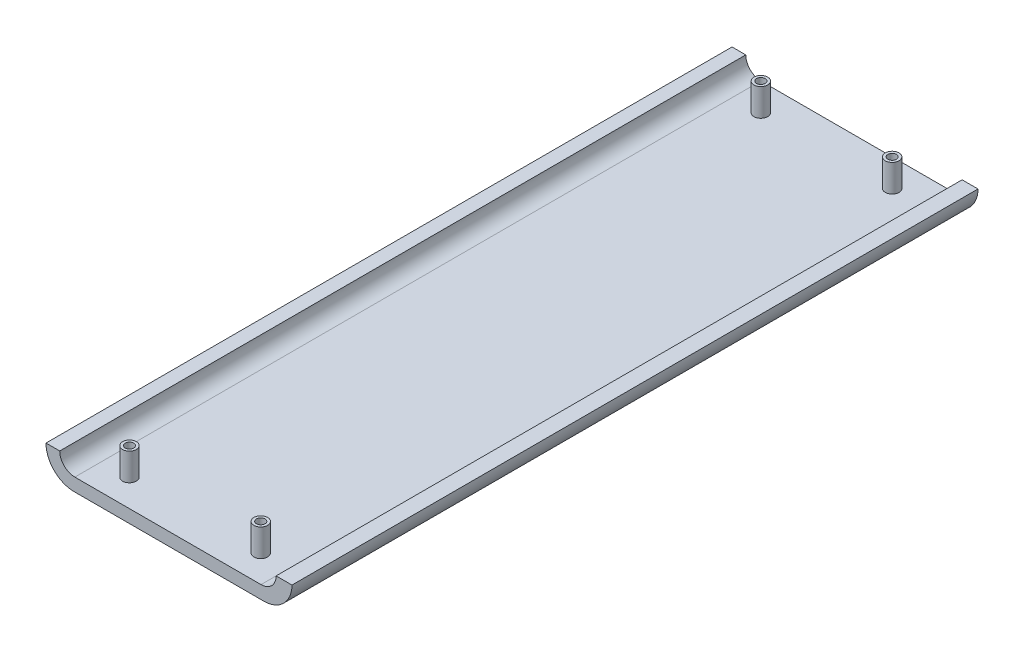
SolidWorks part; units mm, degrees
ref_plane "Front Plane" through (0, 0, 0) normal (0, 0, 1) x (1, 0, 0)
ref_plane "Top Plane" through (0, 0, 0) normal (0, 1, 0) x (1, 0, 0)
ref_plane "Right Plane" through (0, 0, 0) normal (1, 0, 0) x (0, 0, -1)
sketch "Sketch1" plane through (0, 0, 0) normal (0, 0, 1) x (1, 0, 0)
  line L0 (-33.131, 0) -> (2.0171, 0)
  line L1 (-38.3236, 5.1926) -> (-35.7836, 5.1926)
  line L2 (7.2096, 5.1926) -> (4.2721, 5.1926)
  line L3 (1.4781, 2.3986) -> (-32.9896, 2.3986)
  arc A0 (-33.131, 0) -> (-38.3236, 5.1926) centre (-33.131, 5.1926) cw
  arc A1 (2.0171, 0) -> (7.2096, 5.1926) centre (2.0171, 5.1926) ccw
  arc A2 (4.2721, 5.1926) -> (1.4781, 2.3986) centre (1.4781, 5.1926) cw
  arc A3 (-32.9896, 2.3986) -> (-35.7836, 5.1926) centre (-32.9896, 5.1926) cw
extrude "Boss-Extrude1" add sketch "Sketch1" along normal blind 127
sketch "Sketch4" plane through (0, 2.3986, 0) normal (0, 1, 0) x (1, 0, 0)
  circle A0 centre (-27.9096, -5.08) radius 1.27
  circle A1 centre (-3.6019, -5.08) radius 1.27
  circle A2 centre (-27.9096, -121.9649) radius 1.27
  circle A3 centre (-3.6019, -121.9649) radius 1.27
extrude "Boss-Extrude2" add sketch "Sketch4" along normal blind 5.08
hole_wizard "1/16 (0.0625) Diameter Hole1" positions "Sketch7" profile "Sketch6" hole size "1/16" standard "ANSI Inch" end condition up to next
sketch "Sketch7" plane through (0, 7.4786, 0) normal (0, 1, 0) x (1, 0, 0)
  point P0 (-27.9096, -5.08)
  point P3 (-3.6019, -5.08)
  point P6 (-27.9096, -121.9649)
  point P9 (-3.6019, -121.9649)
sketch "Sketch6" plane through (-27.9096, 7.4786, 5.08) normal (1, 0, 0) x (0, 0, 1)
  line L0 (0, 0) -> (0, 7.4786)
  line L1 (0, 7.4786) -> (0.7937, 7.4786)
  line L2 (0.7937, 7.4786) -> (0.7937, 0)
  line L5 (0.7937, 0) -> (0, 0)
  line L11 (0, -6.35) -> (0, 107.95) construction
  dimension "Thru Hole Dia." = 1.5875
  dimension "Thru Hole Depth" = 7.4786
